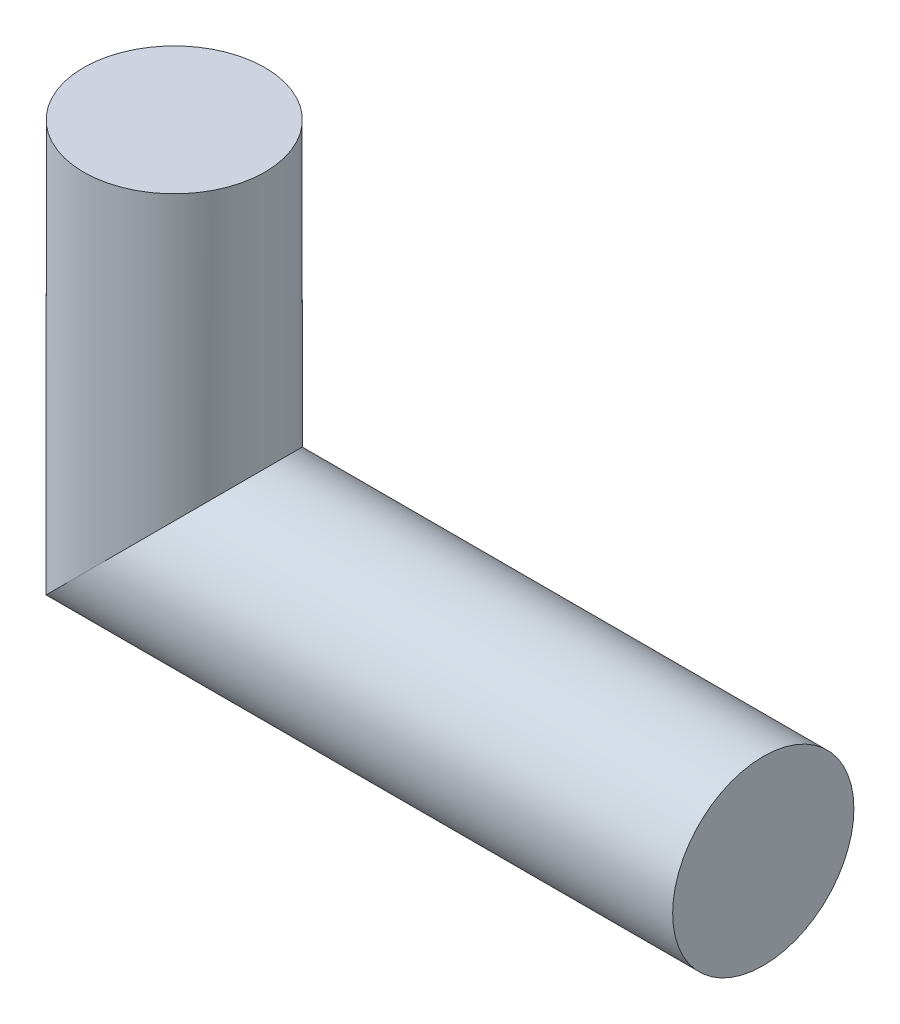
SolidWorks part; units mm, degrees
ref_plane "Front Plane" through (0, 0, 0) normal (0, 0, 1) x (1, 0, 0)
ref_plane "Top Plane" through (0, 0, 0) normal (0, 1, 0) x (1, 0, 0)
ref_plane "Right Plane" through (0, 0, 0) normal (1, 0, 0) x (0, 0, -1)
sketch "Sketch1" plane through (0, 0, 0) normal (1, 0, 0) x (0, 0, -1)
  circle A0 centre (0, 0) radius 6
  dimension "D1" = 12
sketch "Sketch2" plane through (0, 0, 0) normal (0, 0, 1) x (1, 0, 0)
  line L0 (0, 0) -> (-39, 0)
  line L1 (-39, 0) -> (-39, 23)
  dimension "D1" = 39
  dimension "D2" = 23
sweep "Sweep1" add profiles "Sketch1" path "Sketch2"
